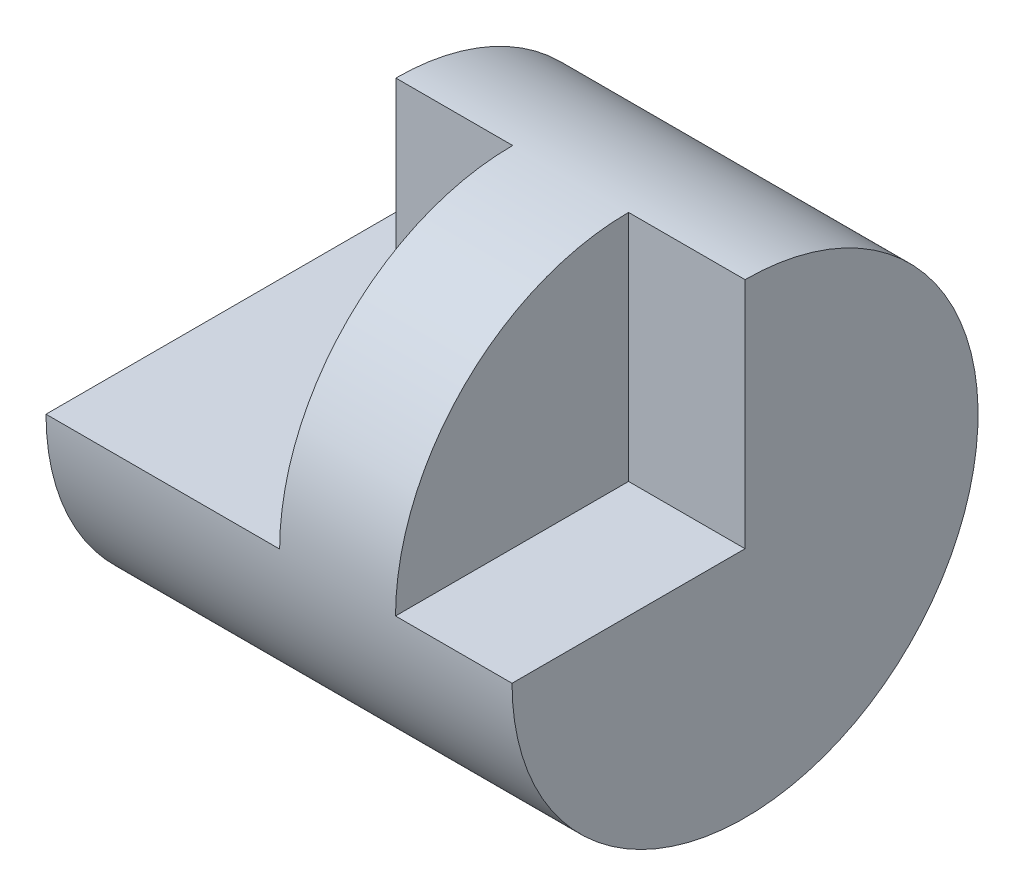
SolidWorks part; units mm, degrees
ref_plane "Front Plane" through (0, 0, 0) normal (0, 0, 1) x (1, 0, 0)
ref_plane "Top Plane" through (0, 0, 0) normal (0, 1, 0) x (1, 0, 0)
ref_plane "Right Plane" through (0, 0, 0) normal (1, 0, 0) x (0, 0, -1)
sketch "Sketch5" plane through (0, 0, 0) normal (0, 0, 1) x (1, 0, 0)
  line L0 (0, 0) -> (4, 0)
  dimension "D1" = 4
revolve "Revolve-Thin2" add sketch "Sketch5" angle 360 about L0 wall 2
sketch "Sketch6" plane through (0, 0, 0) normal (0, 0, 1) x (1, 0, 0)
  line L1 (0, 2) -> (1, 2)
  line L2 (0, 2) -> (0, 0)
  line L3 (0, 0) -> (1, 0)
  line L4 (1, 2) -> (1, 0)
  line L5 (4, 2) -> (3, 2)
  line L6 (4, 2) -> (4, 0)
  line L7 (4, 0) -> (3, 0)
  line L8 (3, 2) -> (3, 0)
  dimension "D1" = 1
  dimension "D2" = 1
  dimension "D3" = 2
  dimension "D4" = 2
extrude "Cut-Extrude5" cut sketch "Sketch6" along normal blind 11 contours L5 L8 L7 L6 | L4 L1 L2 L3
sketch "Sketch7" plane through (0, 0, 0) normal (0, 1, 0) x (1, 0, 0)
  line L1 (2.0054, 0) -> (1, 0)
  line L2 (2.0054, 0) -> (2.0054, -2)
  line L3 (2.0054, -2) -> (1, -2)
  line L4 (1, 0) -> (1, -2)
  dimension "D1" = 2
extrude "Cut-Extrude6" cut sketch "Sketch7" along normal blind 3
sketch "Sketch8" plane through (0, 0, 0) normal (0, 0, 1) x (1, 0, 0)
  line L0 (0, 0) -> (2.0054, 0) construction
  line L1 (0, 2) -> (1.0027, 2)
  line L2 (0, 2) -> (0, 0)
  line L3 (0, 0) -> (1.0027, 0)
  line L4 (1.0027, 2) -> (1.0027, 0)
extrude "Cut-Extrude7" cut sketch "Sketch8" against normal blind 10
